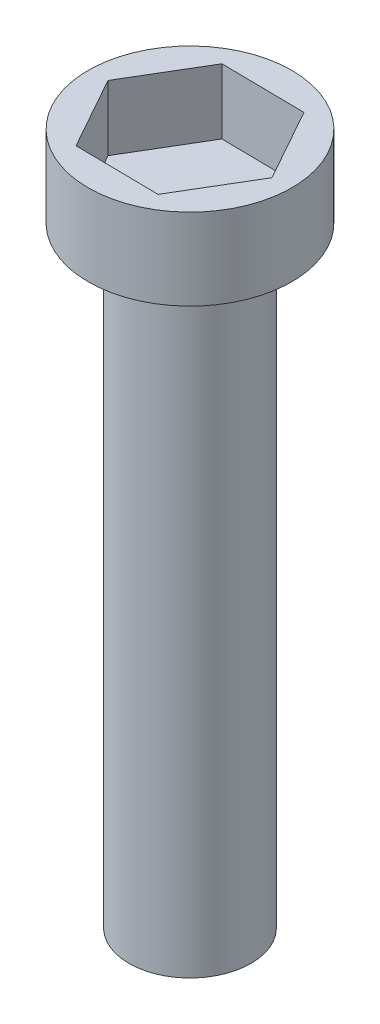
SolidWorks part; units mm, degrees
ref_plane "Front Plane" through (0, 0, 0) normal (0, 0, 1) x (1, 0, 0)
ref_plane "Top Plane" through (0, 0, 0) normal (0, 1, 0) x (1, 0, 0)
ref_plane "Right Plane" through (0, 0, 0) normal (1, 0, 0) x (0, 0, -1)
sketch "Sketch1" plane through (0, 0, 0) normal (0, 1, 0) x (1, 0, 0)
  circle A0 centre (0, 0) radius 1.5
  dimension "D1" = 3
extrude "Boss-Extrude1" add sketch "Sketch1" along normal blind 15
sketch "Sketch2" plane through (0, 15, 0) normal (0, 1, 0) x (1, 0, 0)
  circle A0 centre (0, 0) radius 2.5
  dimension "D1" = 5
extrude "Boss-Extrude2" add sketch "Sketch2" along normal blind 2
sketch "Sketch3" plane through (0, 17, 0) normal (0, 1, 0) x (1, 0, 0)
  line L1 (0.9971, -1.7816) -> (2.0414, -0.0273)
  line L2 (2.0414, -0.0273) -> (1.0443, 1.7543)
  line L3 (1.0443, 1.7543) -> (-0.9971, 1.7816)
  line L4 (-0.9971, 1.7816) -> (-2.0414, 0.0273)
  line L5 (-2.0414, 0.0273) -> (-1.0443, -1.7543)
  line L6 (-1.0443, -1.7543) -> (0.9971, -1.7816)
  circle A0 centre (0, 0) radius 1.7681 construction
extrude "Cut-Extrude2" cut sketch "Sketch3" against normal blind 1.6
